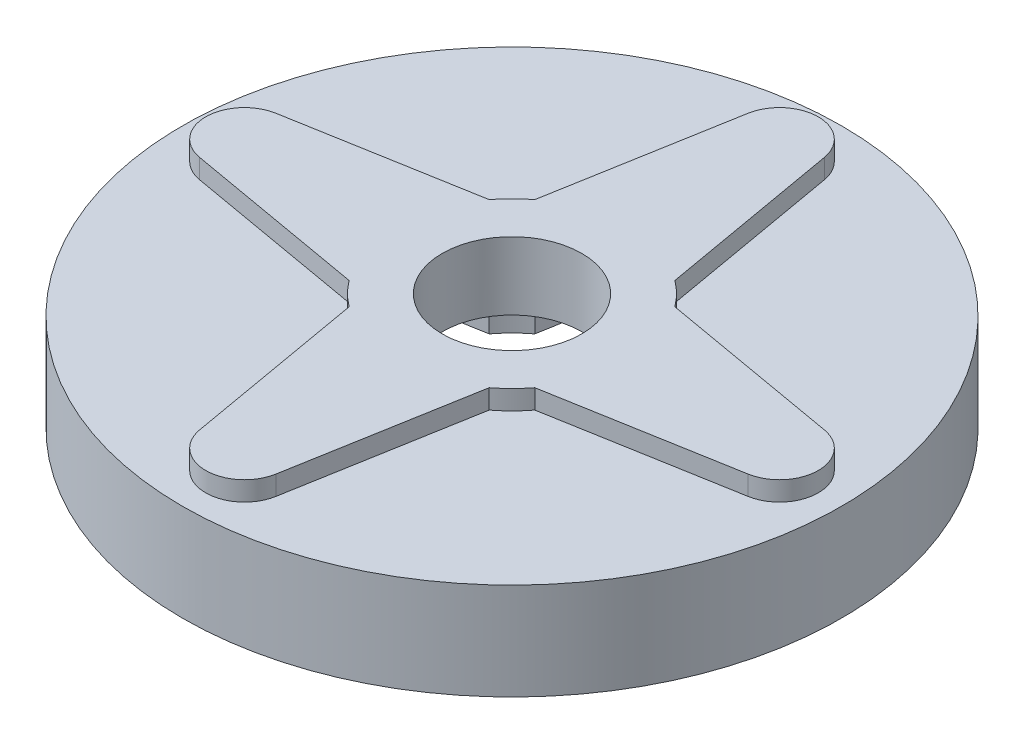
SolidWorks part; units mm, degrees
material "ABS"
ref_plane "Front Plane" through (0, 0, 0) normal (0, 0, 1) x (1, 0, 0)
ref_plane "Top Plane" through (0, 0, 0) normal (0, 1, 0) x (1, 0, 0)
ref_plane "Right Plane" through (0, 0, 0) normal (1, 0, 0) x (0, 0, -1)
sketch "Sketch1" plane through (0, 0, 0) normal (0, 1, 0) x (1, 0, 0)
  line L0 (-1000, 0) -> (49000, 0) construction
  line L1 (0, -1000) -> (0, 49000) construction
  line L2 (7.62, -4.318) -> (7.62, 4.318) construction
  line L3 (7.62, 4.318) -> (17.9652, 2.5017)
  line L4 (7.62, 4.318) -> (6.0843, 4.5876)
  line L5 (7.62, -4.318) -> (17.9652, -2.5017)
  line L6 (7.62, -4.318) -> (6.0843, -4.5876)
  line L7 (-4.318, -7.62) -> (-2.5017, -17.9652)
  line L8 (4.318, -7.62) -> (2.5017, -17.9652)
  line L9 (-4.318, -7.62) -> (-4.5876, -6.0843)
  line L10 (4.318, -7.62) -> (4.5876, -6.0843)
  line L11 (-7.62, 4.318) -> (-17.9652, 2.5017)
  line L12 (-7.62, -4.318) -> (-17.9652, -2.5017)
  line L13 (-7.62, 4.318) -> (-6.0843, 4.5876)
  line L14 (-7.62, -4.318) -> (-6.0843, -4.5876)
  line L15 (4.318, 7.62) -> (2.5017, 17.9652)
  line L16 (-4.318, 7.62) -> (-2.5017, 17.9652)
  line L17 (4.318, 7.62) -> (4.5876, 6.0843)
  line L18 (-4.318, 7.62) -> (-4.5876, 6.0843)
  circle A0 centre (0, 0) radius 21.59
  circle A1 centre (0, 0) radius 7.62
  circle A2 centre (0, 0) radius 4.572
  circle A3 centre (0, 0) radius 20.066
  circle A4 centre (17.526, 0) radius 2.54
  circle A5 centre (0, -17.526) radius 2.54
  circle A6 centre (-17.526, 0) radius 2.54
  circle A7 centre (0, 17.526) radius 2.54
  point P7 (0, 0)
  point P15 (7.62, 0)
  point P47 (0, 0)
  dimension "D1" = 43.18
  dimension "D2" = 15.24
  dimension "D3" = 9.144
  dimension "D4" = 40.132
  dimension "D5" = 5.08
  dimension "D6" = 8.636
  dimension "D7" = 4
extrude "Boss-Extrude1" add sketch "Sketch1" along normal blind 6.35 contours A0
sketch "Sketch2" plane through (0, 0, 0) normal (0, -1, 0) x (1, 0, 0)
  circle A0 centre (0, 0) radius 4.572 construction
  circle A1 centre (0, 0) radius 21.59
  circle A2 centre (0, 0) radius 21.59
  circle A3 centre (0, 0) radius 4.572
  dimension "D1" = 0
extrude "Cut-Extrude1" cut sketch "Sketch2" against normal through all contours A3
sketch "Sketch3" plane through (0, 0, 0) normal (0, -1, 0) x (1, 0, 0)
  line L0 (-7.62, -4.318) -> (-17.9652, -2.5017) construction
  line L1 (-7.62, -4.318) -> (-6.0843, -4.5876) construction
  line L2 (-7.62, 4.318) -> (-6.0843, 4.5876) construction
  line L3 (-7.62, 4.318) -> (-17.9652, 2.5017) construction
  line L4 (-4.318, 7.62) -> (-4.5876, 6.0843) construction
  line L5 (-4.318, 7.62) -> (-2.5017, 17.9652) construction
  line L6 (4.318, 7.62) -> (2.5017, 17.9652) construction
  line L7 (4.318, 7.62) -> (4.5876, 6.0843) construction
  line L8 (7.62, 4.318) -> (6.0843, 4.5876) construction
  line L9 (7.62, 4.318) -> (17.9652, 2.5017) construction
  line L10 (7.62, -4.318) -> (17.9652, -2.5017) construction
  line L11 (7.62, -4.318) -> (6.0843, -4.5876) construction
  line L12 (4.318, -7.62) -> (4.5876, -6.0843) construction
  line L13 (4.318, -7.62) -> (2.5017, -17.9652) construction
  line L14 (-4.318, -7.62) -> (-2.5017, -17.9652) construction
  line L15 (-7.62, -4.318) -> (-17.9652, -2.5017)
  line L16 (-7.62, -4.318) -> (-6.0843, -4.5876)
  line L17 (-7.62, 4.318) -> (-6.0843, 4.5876)
  line L18 (-7.62, 4.318) -> (-17.9652, 2.5017)
  line L19 (-4.318, 7.62) -> (-4.5876, 6.0843)
  line L20 (-4.318, 7.62) -> (-2.5017, 17.9652)
  line L21 (4.318, 7.62) -> (2.5017, 17.9652)
  line L22 (4.318, 7.62) -> (4.5876, 6.0843)
  line L23 (7.62, 4.318) -> (6.0843, 4.5876)
  line L24 (7.62, 4.318) -> (17.9652, 2.5017)
  line L25 (7.62, -4.318) -> (17.9652, -2.5017)
  line L26 (7.62, -4.318) -> (6.0843, -4.5876)
  line L27 (4.318, -7.62) -> (4.5876, -6.0843)
  line L28 (4.318, -7.62) -> (2.5017, -17.9652)
  line L29 (-4.318, -7.62) -> (-2.5017, -17.9652)
  line L30 (-4.318, -7.62) -> (-4.5876, -6.0843) construction
  line L31 (-4.318, -7.62) -> (-4.5876, -6.0843)
  circle A1 centre (-17.526, 0) radius 2.54 construction
  circle A2 centre (0, 0) radius 21.59
  circle A3 centre (0, 0) radius 21.59
  circle A4 centre (0, 17.526) radius 2.54 construction
  circle A5 centre (17.526, 0) radius 2.54 construction
  circle A6 centre (0, 0) radius 7.62 construction
  circle A7 centre (0, -17.526) radius 2.54 construction
  circle A8 centre (-17.526, 0) radius 2.54
  circle A9 centre (0, 17.526) radius 2.54
  circle A10 centre (17.526, 0) radius 2.54
  circle A11 centre (0, 0) radius 7.62
  circle A12 centre (0, -17.526) radius 2.54
  circle M2 centre (0, 0) radius 4.572
  dimension "D1" = 0
extrude "Cut-Extrude2" cut sketch "Sketch3" against normal blind 3.175 contours A12 L28 L27 A11 L31 L29 | A12 | A11 L17 L18 A8 L15 L16 | A8 | A11 M2 | A11 L22 L21 A9 L20 L19 | A9 | A10 | A11 L26 L25 A10 L24 L23
sketch "Sketch4" plane through (0, 6.35, 0) normal (0, 1, 0) x (1, 0, 0)
  line L0 (4.318, -7.62) -> (2.5017, -17.9652) construction
  line L1 (4.318, -7.62) -> (4.5876, -6.0843) construction
  line L2 (-4.318, -7.62) -> (-2.5017, -17.9652) construction
  line L3 (-4.318, -7.62) -> (-4.5876, -6.0843) construction
  line L4 (7.62, -4.318) -> (17.9652, -2.5017) construction
  line L5 (7.62, -4.318) -> (6.0843, -4.5876) construction
  line L6 (7.62, 4.318) -> (17.9652, 2.5017) construction
  line L7 (7.62, 4.318) -> (6.0843, 4.5876) construction
  line L8 (-4.318, 7.62) -> (-2.5017, 17.9652) construction
  line L9 (-4.318, 7.62) -> (-4.5876, 6.0843) construction
  line L10 (4.318, 7.62) -> (2.5017, 17.9652) construction
  line L11 (4.318, 7.62) -> (4.5876, 6.0843) construction
  line L12 (-7.62, -4.318) -> (-17.9652, -2.5017) construction
  line L13 (-7.62, -4.318) -> (-6.0843, -4.5876) construction
  line L14 (-7.62, 4.318) -> (-17.9652, 2.5017) construction
  line L15 (-7.62, 4.318) -> (-6.0843, 4.5876) construction
  line L16 (4.318, -7.62) -> (2.5017, -17.9652)
  line L17 (4.318, -7.62) -> (4.5876, -6.0843)
  line L18 (-4.318, -7.62) -> (-2.5017, -17.9652)
  line L19 (-4.318, -7.62) -> (-4.5876, -6.0843)
  line L20 (7.62, -4.318) -> (17.9652, -2.5017)
  line L21 (7.62, -4.318) -> (6.0843, -4.5876)
  line L22 (7.62, 4.318) -> (17.9652, 2.5017)
  line L23 (7.62, 4.318) -> (6.0843, 4.5876)
  line L24 (-4.318, 7.62) -> (-2.5017, 17.9652)
  line L25 (-4.318, 7.62) -> (-4.5876, 6.0843)
  line L26 (4.318, 7.62) -> (2.5017, 17.9652)
  line L27 (4.318, 7.62) -> (4.5876, 6.0843)
  line L28 (-7.62, -4.318) -> (-17.9652, -2.5017)
  line L29 (-7.62, -4.318) -> (-6.0843, -4.5876)
  line L30 (-7.62, 4.318) -> (-17.9652, 2.5017)
  line L31 (-7.62, 4.318) -> (-6.0843, 4.5876)
  circle A1 centre (0, 0) radius 21.59
  circle A2 centre (0, 0) radius 21.59
  circle A3 centre (17.526, 0) radius 2.54
  circle A4 centre (17.526, 0) radius 2.54
  circle A5 centre (0, 0) radius 20.066
  circle A6 centre (0, 0) radius 20.066
  circle A7 centre (0, 0) radius 4.572
  circle A8 centre (0, 0) radius 4.572
  circle A9 centre (0, 0) radius 7.62
  circle A10 centre (0, 0) radius 7.62
  circle A11 centre (0, 0) radius 21.59
  circle A12 centre (0, 0) radius 21.59
  circle A13 centre (0, -17.526) radius 2.54
  circle A14 centre (0, -17.526) radius 2.54
  circle A15 centre (0, 17.526) radius 2.54
  circle A16 centre (0, 17.526) radius 2.54
  circle A17 centre (-17.526, 0) radius 2.54
  circle A18 centre (-17.526, 0) radius 2.54
  circle M10 centre (0, 0) radius 4.572
  dimension "D1" = 0
  dimension "D2" = 0
  dimension "D3" = 0
  dimension "D4" = 0
  dimension "D5" = 0
  dimension "D6" = 0
  dimension "D7" = 0
  dimension "D8" = 0
  dimension "D9" = 0
extrude "Boss-Extrude2" add sketch "Sketch4" along normal blind 1.27 contours A16 L24 L25 A10 L27 L26 | A16 | A18 L28 L29 A10 L31 L30 | A18 | A14 | A14 L16 L17 A10 L19 L18 | A10 L21 L20 A4 L22 L23 | A4 | A10 M10
